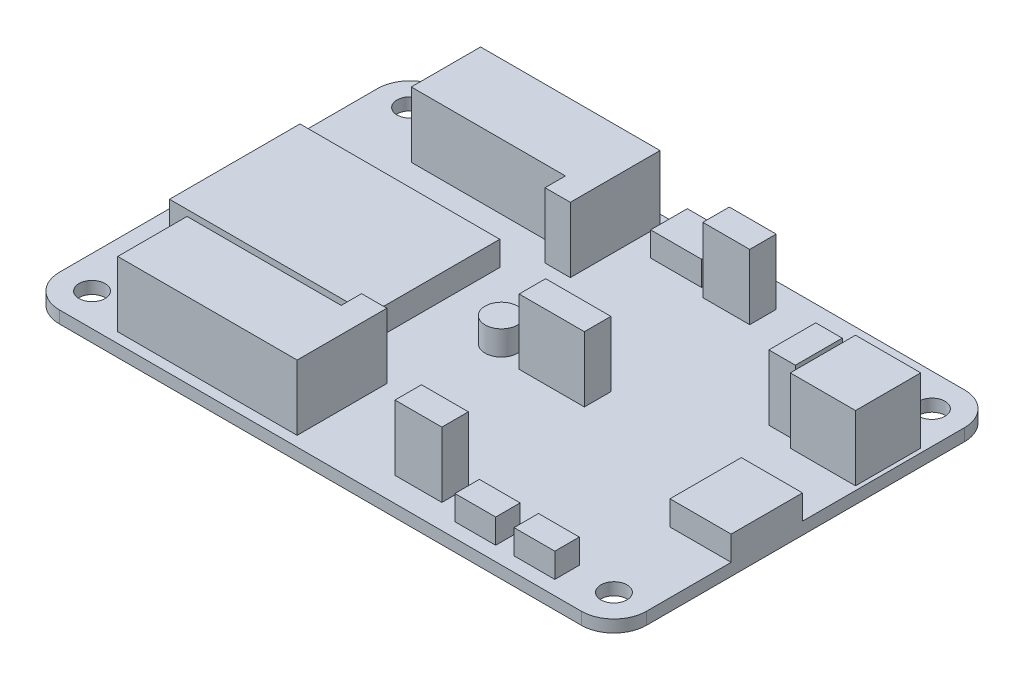
SolidWorks part; units mm, degrees
other "Marca1"
sketch "Croquis4" plane through (36, 9.5, 23.5) normal (0, 1, 0) x (0, 0, 1)
material "Caucho"
ref_plane "Alzado" through (0, 0, 0) normal (0, 0, 1) x (1, 0, 0)
ref_plane "Planta" through (0, 0, 0) normal (0, 1, 0) x (1, 0, 0)
ref_plane "Vista lateral" through (0, 0, 0) normal (1, 0, 0) x (0, 0, -1)
sketch "Croquis1" plane through (0, 0, 0) normal (0, 1, 0) x (1, 0, 0)
  line L1 (-36, -23.5) -> (36, -23.5)
  line L2 (-36, -23.5) -> (-36, 23.5)
  line L3 (-36, 23.5) -> (36, 23.5)
  line L4 (36, -23.5) -> (36, 23.5)
  line L5 (-36, -23.5) -> (36, 23.5) construction
  line L6 (-36, 23.5) -> (36, -23.5) construction
  point P0 (0, 0)
  dimension "D1" = 72
  dimension "D2" = 47
extrude "Saliente-Extruir1" add sketch "Croquis1" along normal blind 1.5
sketch "Croquis2" plane through (0, 1.5, 0) normal (0, 1, 0) x (1, 0, 0)
  line L1 (-32, -19.5) -> (32, -19.5) construction
  line L2 (-32, -19.5) -> (-32, 19.5) construction
  line L3 (-32, 19.5) -> (32, 19.5) construction
  line L4 (32, -19.5) -> (32, 19.5) construction
  line L5 (-32, -19.5) -> (32, 19.5) construction
  line L6 (-32, 19.5) -> (32, -19.5) construction
  circle A4 centre (-32, 19.5) radius 1.6
  circle A5 centre (32, 19.5) radius 1.6
  circle A6 centre (32, -19.5) radius 1.6
  circle A7 centre (-32, -19.5) radius 1.6
  point P0 (0, 0)
  dimension "D1" = 3.2
  dimension "D2" = 39
  dimension "D3" = 64
extrude "Cortar-Extruir1" cut sketch "Croquis2" against normal through all
fillet "Redondeo1" radius 4 4 edges at (-36, 0.75, 23.5) (-36, 0.75, -23.5) (36, 0.75, -23.5) (36, 0.75, 23.5)
sketch "Croquis3" plane through (0, 1.5, 0) normal (0, 1, 0) x (1, 0, 0)
  line L0 (-4.1, 11.25) -> (-7.2, 11.25)
  line L1 (-26.1, 22.25) -> (-4.1, 22.25)
  line L2 (-26.1, 22.25) -> (-26.1, 13.75)
  line L4 (-4.1, 22.25) -> (-4.1, 11.25)
  line L9 (-7.2, 11.25) -> (-7.2, 13.75)
  line L10 (32, 23.5) -> (-32, 23.5) construction
  line L22 (51.6667, 238) -> (258.3333, 238) construction
  line L23 (52.1758, 186.7939) -> (52.1758, 141.6663) construction
  line L24 (-7.2, 13.75) -> (-26.1, 13.75)
  line L25 (-36, 0) -> (36, 0) construction
  line L26 (36, -19.5) -> (36, 19.5) construction
  line L27 (-36, 19.5) -> (-36, -19.5) construction
  line L28 (11.9, -20.5) -> (11.9, -17.25)
  line L29 (6.15, 20.5) -> (11.9, 20.5)
  line L30 (6.15, 20.5) -> (6.15, 17.25)
  line L31 (6.15, 17.25) -> (11.9, 17.25)
  line L32 (11.9, 20.5) -> (11.9, 17.25)
  line L33 (6.15, -17.25) -> (11.9, -17.25)
  line L34 (6.15, -20.5) -> (6.15, -17.25)
  line L35 (6.15, -20.5) -> (11.9, -20.5)
  line L36 (-7.2, -13.75) -> (-26.1, -13.75)
  line L37 (-7.2, -11.25) -> (-7.2, -13.75)
  line L38 (-4.1, -22.25) -> (-4.1, -11.25)
  line L39 (-26.1, -22.25) -> (-26.1, -13.75)
  line L40 (-26.1, -22.25) -> (-4.1, -22.25)
  line L41 (-4.1, -11.25) -> (-7.2, -11.25)
  line L42 (23.75, 13.5) -> (27, 13.5)
  line L43 (23.75, 13.5) -> (23.75, 7.75)
  line L44 (23.75, 7.75) -> (27, 7.75)
  line L45 (27, 13.5) -> (27, 7.75)
  line L46 (27, 10.625) -> (27.5, 10.625) construction
  line L47 (27.5, 14.625) -> (35.5, 14.625)
  line L48 (27.5, 14.625) -> (27.5, 6.625)
  line L49 (27.5, 6.625) -> (35.5, 6.625)
  line L50 (35.5, 14.625) -> (35.5, 6.625)
  line L52 (2.5, -1.625) -> (10.5, -1.625)
  line L53 (2.5, -1.625) -> (2.5, 1.625)
  line L54 (2.5, 1.625) -> (10.5, 1.625)
  line L55 (10.5, -1.625) -> (10.5, 1.625)
  line L56 (2.5, -1.625) -> (10.5, 1.625) construction
  line L57 (2.5, 1.625) -> (10.5, -1.625) construction
  point P14 (0, 0)
  point P46 (6.5, 0)
  dimension "D1" = 8.5
  dimension "D2" = 22
  dimension "D3" = 1.25
  dimension "D4" = 3.1
  dimension "D5" = 9.9
  dimension "D6" = 5.75
  dimension "D7" = 3
  dimension "D8" = 10.25
  dimension "D9" = 3.25
  dimension "D10" = 5.75
  dimension "D11" = 2.5
  dimension "D12" = 3.25
  dimension "D13" = 9
  dimension "D14" = 10
  dimension "D15" = 0.5
  dimension "D16" = 8
  dimension "D17" = 8
  dimension "D18" = 3.25
  dimension "D19" = 8
  dimension "D20" = 2.5
extrude "Saliente-Extruir2" add sketch "Croquis3" along normal blind 8
sketch "Croquis6" plane through (0, 1.5, 0) normal (0, 1, 0) x (1, 0, 0)
  line L0 (202.3191, -28.3409) -> (202.3191, -235.0075) construction
  line L1 (36, 0) -> (-36, 0) construction
  line L2 (-36, 19.5) -> (-36, -19.5) construction
  line L3 (36, -19.5) -> (36, 19.5) construction
  line L4 (28.5, -0.375) -> (36, -0.375)
  line L5 (28.5, -0.375) -> (28.5, -9.1247)
  line L6 (28.5, -9.1247) -> (36, -9.1247)
  line L7 (36, -0.375) -> (36, -9.1247)
  line L8 (-32, -23.5) -> (32, -23.5) construction
  line L9 (14.7488, -18.75) -> (19.7488, -18.75)
  line L10 (14.7488, -18.75) -> (14.7488, -21.75)
  line L11 (14.7488, -21.75) -> (19.7488, -21.75)
  line L12 (19.7488, -18.75) -> (19.7488, -21.75)
  line L13 (22, -18.75) -> (27, -18.75)
  line L14 (22, -18.75) -> (22, -21.75)
  line L15 (22, -21.75) -> (27, -21.75)
  line L16 (27, -18.75) -> (27, -21.75)
  line L17 (32, 23.5) -> (-32, 23.5) construction
  line L18 (-1.25, 22.75) -> (5, 22.75)
  line L19 (-1.25, 22.75) -> (-1.25, 18.25)
  line L20 (-1.25, 18.25) -> (5, 18.25)
  line L21 (5, 22.75) -> (5, 18.25)
  line L23 (-34, -8) -> (-9.5, -8)
  line L24 (-34, -8) -> (-34, 8)
  line L25 (-34, 8) -> (-9.5, 8)
  line L26 (-9.5, -8) -> (-9.5, 8)
  line L27 (-34, -8) -> (-9.5, 8) construction
  line L28 (-34, 8) -> (-9.5, -8) construction
  circle A0 centre (-1.3, 0) radius 2
  point P11 (0, 0)
  point P33 (-21.75, 0)
  dimension "D1" = 4
  dimension "D2" = 1.3
  dimension "D3" = 8.7497
  dimension "D4" = 7.5
  dimension "D5" = 0.75
  dimension "D6" = 5
  dimension "D7" = 3
  dimension "D8" = 2.2512
  dimension "D9" = 9
  dimension "D10" = 1.75
  dimension "D11" = 0.75
  dimension "D12" = 4.5
  dimension "D13" = 6.25
  dimension "D14" = 31
  dimension "D15" = 16
  dimension "D16" = 2
  dimension "D17" = 24.5
extrude "Saliente-Extruir3" add sketch "Croquis6" along normal blind 3
